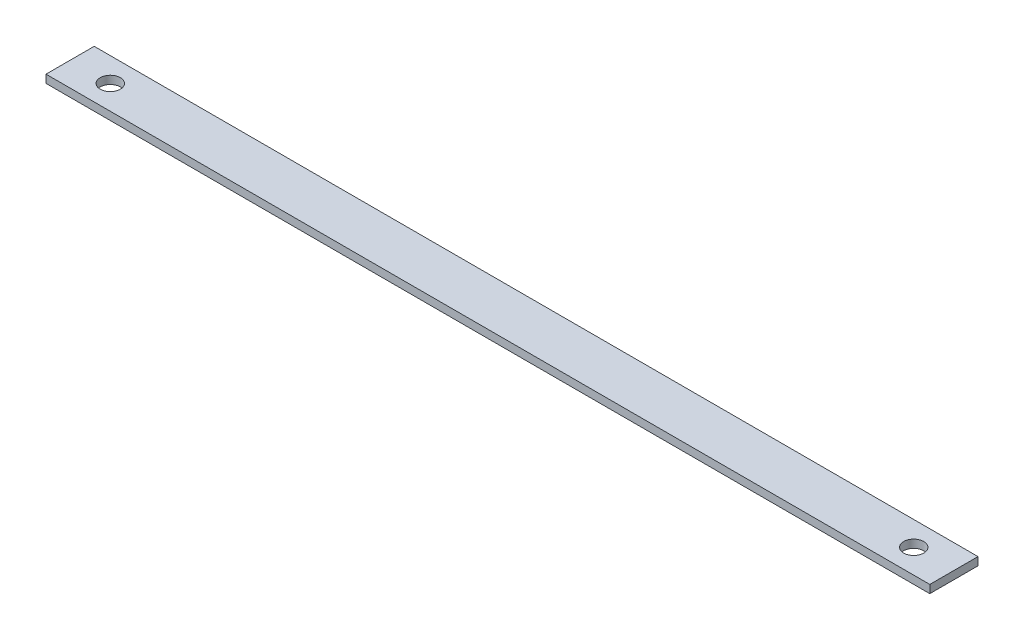
SolidWorks part; units mm, degrees
ref_plane "Front Plane" through (0, 0, 0) normal (0, 0, 1) x (1, 0, 0)
ref_plane "Top Plane" through (0, 0, 0) normal (0, 1, 0) x (1, 0, 0)
ref_plane "Right Plane" through (0, 0, 0) normal (1, 0, 0) x (0, 0, -1)
sketch "Sketch1" plane through (0, 0, 0) normal (0, 1, 0) x (1, 0, 0)
  line L1 (-110, -6) -> (110, -6)
  line L2 (-110, -6) -> (-110, 6)
  line L3 (-110, 6) -> (110, 6)
  line L4 (110, -6) -> (110, 6)
  line L5 (-110, -6) -> (110, 6) construction
  line L6 (-110, 6) -> (110, -6) construction
  point P0 (0, 0)
  dimension "D1" = 12
  dimension "D2" = 220
extrude "Boss-Extrude1" add sketch "Sketch1" along normal blind 2
sketch "Sketch2" plane through (0, 2, 0) normal (0, 1, 0) x (1, 0, 0)
  line L0 (-93.3786, 0) -> (99.7379, 0) construction
  line L1 (0, 28.8342) -> (0, -18.9283) construction
  point P5 (100, 0)
  point P6 (-100, 0)
  dimension "D1" = 100
hole_wizard "Ø5.0mm Dowel Hole1" positions "Sketch3" profile "Sketch4" hole size "Ø5.0" standard "ANSI Metric" end condition up to next
sketch "Sketch3" plane through (0, 2, 0) normal (0, 1, 0) x (1, 0, 0)
  point P0 (-100, 0)
  point P3 (100, 0)
sketch "Sketch4" plane through (-100, 2, 0) normal (1, 0, 0) x (0, 0, 1)
  line L0 (0, 0) -> (0, 2)
  line L1 (0, 2) -> (2.5, 2)
  line L2 (2.5, 2) -> (2.5, 0)
  line L5 (2.5, 0) -> (0, 0)
  line L11 (0, -6.35) -> (0, 107.95) construction
  dimension "Thru Hole Dia." = 5
  dimension "Thru Hole Depth" = 2
equation "\"Width\"=12"
equation "\"Length\"= 200"
equation "\"D2@Sketch1\"=\"Length\"+20"
equation "\"thick\"= 2"
equation "\"D1@Boss-Extrude1\"=\"thick\""
equation "\"D1@Sketch2\"=\"Length\"/2"
equation "\"D1@Sketch1\"=\"Width\""
